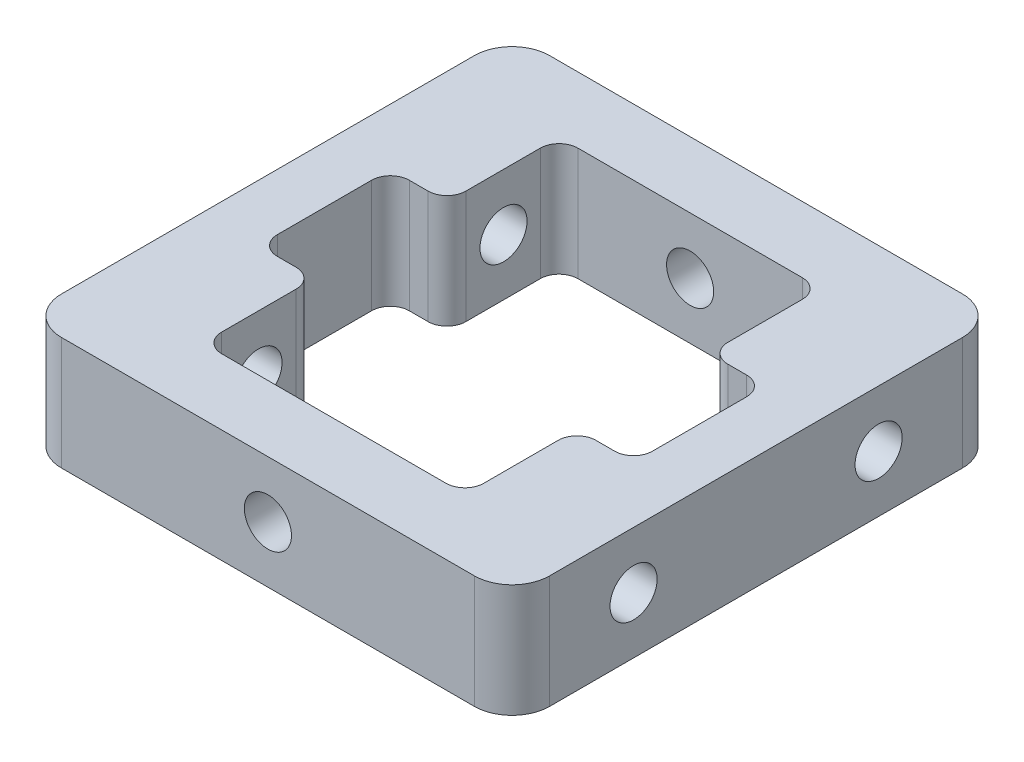
SolidWorks part; units mm, degrees
material "6063-T5"
ref_plane "前视基准面" through (0, 0, 0) normal (0, 0, 1) x (1, 0, 0)
ref_plane "上视基准面" through (0, 0, 0) normal (0, 1, 0) x (1, 0, 0)
ref_plane "右视基准面" through (0, 0, 0) normal (1, 0, 0) x (0, 0, -1)
other "Configuration Table"
sketch "草图1" plane through (0, 0, 0) normal (0, 0, 1) x (1, 0, 0)
  line L1 (-12.95, -12.95) -> (12.95, -12.95)
  line L2 (-12.95, -12.95) -> (-12.95, 12.95)
  line L3 (-12.95, 12.95) -> (12.95, 12.95)
  line L4 (12.95, -12.95) -> (12.95, 12.95)
  line L5 (-12.95, -12.95) -> (12.95, 12.95) construction
  line L6 (-12.95, 12.95) -> (12.95, -12.95) construction
  point P0 (0, 0)
  dimension "D1" = 25.9
extrude "凸台-拉伸1" add sketch "草图1" along normal blind 25.9
sketch "草图2" plane through (0, 0, 25.9) normal (0, 0, 1) x (1, 0, 0)
  line L1 (-7.5, -7.5) -> (7.5, -7.5) construction
  line L2 (-7.5, -7.5) -> (-7.5, 7.5) construction
  line L3 (-7.5, 7.5) -> (7.5, 7.5) construction
  line L4 (7.5, -7.5) -> (7.5, 7.5) construction
  line L5 (-7.5, -7.5) -> (7.5, 7.5) construction
  line L6 (-7.5, 7.5) -> (7.5, -7.5) construction
  circle A0 centre (-7.5, 7.5) radius 2.025
  circle A1 centre (-7.5, -7.5) radius 2.025
  circle A2 centre (7.5, -7.5) radius 2.025
  circle A3 centre (7.5, 7.5) radius 2.025
  point P0 (0, 0)
  dimension "D1" = 4.05
  dimension "D2" = 15
  dimension "D3" = 15
sketch "草图3" plane through (12.95, 0, 0) normal (1, 0, 0) x (0, 0, -1)
  line L0 (-12.95, 12.95) -> (-12.95, -12.95) construction
  line L1 (-25.9, 12.95) -> (0, 12.95) construction
  line L2 (-25.9, -12.95) -> (0, -12.95) construction
  circle A0 centre (-19.45, 0) radius 1.525
  circle A1 centre (-6.45, 0) radius 1.525
  dimension "D1" = 3.05
  dimension "D2" = 13
hole_wizard "M3 螺纹孔1" positions "3D草图1" profile "草图4" tap size "M3" standard "GB" end condition through all
sketch3d "3D草图1"
  point P0 (12.95, 0, 19.45)
  point P3 (12.95, 0, 6.45)
sketch "草图4" plane through (12.95, 0, 19.45) normal (0, 1, 0) x (0, 0, -1)
  line L0 (0, 0) -> (0, 25.9)
  line L1 (0, 25.9) -> (1.25, 25.9)
  line L2 (1.25, 25.9) -> (1.25, 0)
  line L5 (1.25, 0) -> (0, 0)
  line L11 (0, -6.35) -> (0, 107.95) construction
  dimension "通孔螺纹孔钻头直径" = 2.5
  dimension "通孔螺纹孔钻头深度" = 25.9
cosmetic thread "孔螺蚊线1" parameters "D2"=3
cosmetic thread "孔螺蚊线2" parameters "D2"=3
sketch "草图6" plane through (-12.95, 0, 0) normal (-1, 0, 0) x (0, 0, 1)
  line L0 (25.9, -12.95) -> (0, -12.95) construction
  line L1 (8.95, -12.95) -> (16.95, -12.95)
  line L2 (8.95, -12.95) -> (8.95, 4.95)
  line L3 (8.95, 4.95) -> (16.95, 4.95)
  line L4 (16.95, -12.95) -> (16.95, 4.95)
  line L5 (12.95, 12.95) -> (12.95, 4.95) construction
  line L6 (25.9, 12.95) -> (0, 12.95) construction
  dimension "D1" = 8
  dimension "D2" = 8
sketch "草图7" plane through (-12.95, 0, 0) normal (-1, 0, 0) x (0, 0, 1)
  line L11 (25.9, 12.95) -> (25.9, -12.95) construction
  line L12 (0, -3) -> (25.9, -3)
  line L13 (0, -3) -> (0, 3)
  line L14 (0, 3) -> (25.9, 3)
  line L15 (25.9, -3) -> (25.9, 3)
  line L16 (0, -3) -> (25.9, 3) construction
  line L17 (0, 3) -> (25.9, -3) construction
  line L18 (0, 12.95) -> (0, -12.95) construction
  line L19 (25.9, 3) -> (25.9, -3)
  line L20 (0, 3) -> (0, -3)
  point P22 (12.95, 0)
  line M6 (0, 12.95) -> (0, -12.95)
  line M7 (0, -12.95) -> (25.9, -12.95)
  line M8 (25.9, -12.95) -> (25.9, 12.95)
  line M9 (25.9, 12.95) -> (0, 12.95)
  dimension "D1" = 6
extrude "切除-拉伸4" cut sketch "草图7" against normal through all contours L14 M6 M8 M9 | L12 M6 M7 M8
fillet "圆角1" radius 2 4 edges at (12.95, 0, 0) (12.95, 0, 25.9) (-12.95, 0, 25.9) (-12.95, 0, 0)
sketch "草图8" plane through (0, 3, 0) normal (0, 1, 0) x (1, 0, 0)
  line L0 (-12.95, -12.95) -> (12.95, -12.95) construction
  line L5 (-12.95, -2) -> (-12.95, -23.9) construction
  line L6 (12.95, -2) -> (12.95, -23.9) construction
  line L9 (-12.95, -9.45) -> (-6.95, -9.45)
  line L10 (-6.95, -9.45) -> (-6.95, -3.5)
  line L11 (-6.95, -3.5) -> (6.95, -3.5)
  line L12 (6.95, -3.5) -> (6.95, -9.45)
  line L13 (6.95, -9.45) -> (12.95, -9.45)
  line L16 (10.95, 0) -> (-10.95, 0) construction
  line L17 (6.95, -16.45) -> (12.95, -16.45)
  line L18 (6.95, -22.4) -> (6.95, -16.45)
  line L19 (-6.95, -22.4) -> (6.95, -22.4)
  line L20 (-6.95, -16.45) -> (-6.95, -22.4)
  line L21 (-12.95, -16.45) -> (-6.95, -16.45)
  line L22 (-9.95, -9.45) -> (-9.95, -16.45)
  line L23 (9.95, -9.45) -> (9.95, -16.45)
  dimension "D1" = 6
  dimension "D2" = 3.5
  dimension "D3" = 6
  dimension "D4" = 3.5
  dimension "D5" = 3.5
extrude "切除-拉伸5" cut sketch "草图8" against normal through all both contours L22 L0 L23 L13 L12 L11 L10 L9 | L0 L22 L21 L20 L19 L18 L17 L23
fillet "圆角3" radius 1 12 edges at (-9.95, 0, 9.45) (-6.95, 0, 9.45) (-6.95, 0, 3.5) (6.95, 0, 3.5) (6.95, 0, 22.4) (-6.95, 0, 22.4) (-6.95, 0, 16.45) (-9.95, 0, 16.45) (9.95, 0, 9.45) (9.95, 0, 16.45) (6.95, 0, 16.45) (6.95, 0, 9.45)
sketch "草图9" plane through (0, 0, 25.9) normal (0, 0, 1) x (1, 0, 0)
  point P0 (0, 0)
hole_wizard "M3 螺纹孔2" positions "3D草图2" profile "草图10" tap size "M3" standard "GB" end condition through all
sketch3d "3D草图2"
  point P0 (0, 0, 0)
  point P3 (0, 0, 25.9)
sketch "草图10" plane through (0, 0, 25.9) normal (1, 0, 0) x (0, -1, 0)
  line L0 (0, 0) -> (0, 25.9)
  line L1 (0, 25.9) -> (1.25, 25.9)
  line L2 (1.25, 25.9) -> (1.25, 0)
  line L5 (1.25, 0) -> (0, 0)
  line L11 (0, -6.35) -> (0, 107.95) construction
  dimension "通孔螺纹孔钻头直径" = 2.5
  dimension "通孔螺纹孔钻头深度" = 25.9
cosmetic thread "孔螺蚊线3" parameters "D2"=3
cosmetic thread "孔螺蚊线4" parameters "D2"=3
